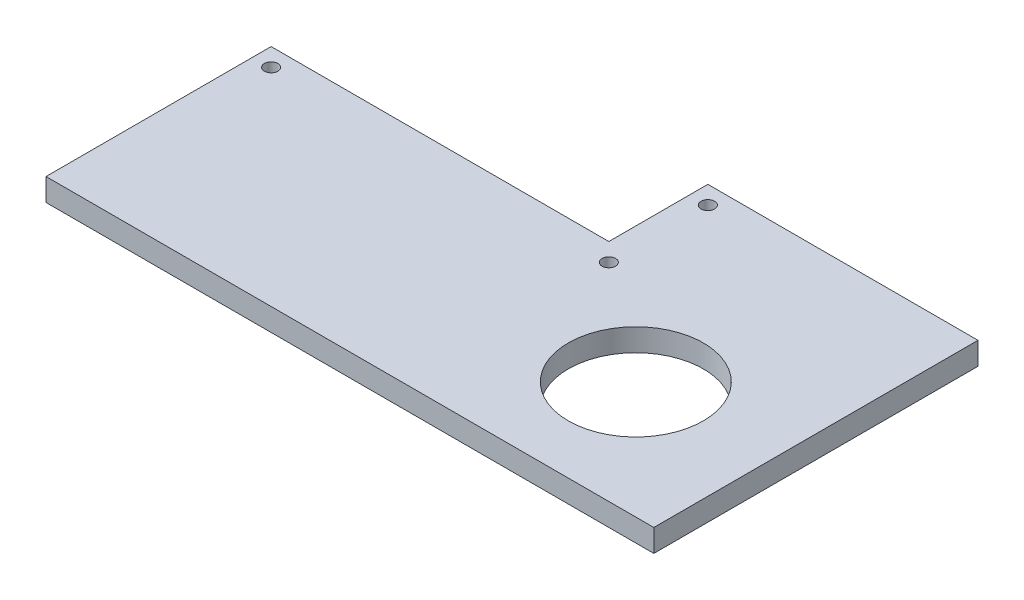
SolidWorks part; units mm, degrees
ref_plane "前视基准面" through (0, 0, 0) normal (0, 0, 1) x (1, 0, 0)
ref_plane "上视基准面" through (0, 0, 0) normal (0, 1, 0) x (1, 0, 0)
ref_plane "右视基准面" through (0, 0, 0) normal (1, 0, 0) x (0, 0, -1)
sketch "Sketch1" plane through (0, 0, 0) normal (0, 1, 0) x (1, 0, 0)
  line L0 (-41.5, -7) -> (33.5, -7)
  line L1 (-37.5, 11) -> (37.5, 11) construction
  line L2 (-37.5, 11) -> (-37.5, -11) construction
  line L3 (-37.5, -11) -> (37.5, -11) construction
  line L4 (37.5, 11) -> (37.5, -11) construction
  line L5 (-37.5, 11) -> (37.5, -11) construction
  line L6 (-37.5, -11) -> (37.5, 11) construction
  line L7 (33.5, -7) -> (33.5, 15)
  line L8 (33.5, 15) -> (93.5, 15)
  line L9 (93.5, 15) -> (93.5, -57)
  line L10 (93.5, -57) -> (-41.5, -57)
  line L11 (-41.5, -57) -> (-41.5, -7)
  line L12 (63.5, 15) -> (63.5, -57) construction
  circle A0 centre (-37.5, -11) radius 1.5
  circle A1 centre (37.5, -11) radius 1.5
  circle A2 centre (37.5, 11) radius 1.5
  circle A3 centre (63.5, -31) radius 15
  point P0 (0, 0)
  dimension "D3" = 3
  dimension "D4" = 3
  dimension "D5" = 3
  dimension "D10" = 20
  dimension "D11" = 30
  dimension "D1" = 22
  dimension "D2" = 75
  dimension "D6" = 4
  dimension "D7" = 4
  dimension "D8" = 4
  dimension "D9" = 4
  dimension "D12" = 30
  dimension "D13" = 30
  dimension "D14" = 50
extrude "Boss-Extrude1" add sketch "Sketch1" along normal blind 5
sketch "Sketch2" plane through (0, 5, 0) normal (0, 1, 0) x (1, 0, 0)
  line L0 (-41.5, -26.1386) -> (33.5, -26.1386) construction
  line L1 (-41.5, -39.5089) -> (33.5, -39.5089) construction
  line L2 (-41.5, -7) -> (-41.5, -57) construction
  line L3 (33.5, -7) -> (33.5, -57) construction
  line L4 (-41.5, -57) -> (93.5, -57) construction
  text T0 "ISDN3002 MEC" font "黑体" height in points 26
  text T1 "Trocomotor\r\nFollower" font "黑体" height in points 26
extrude "Cut-Extrude1" [suppressed] cut sketch "Sketch2" against normal blind 0.1
